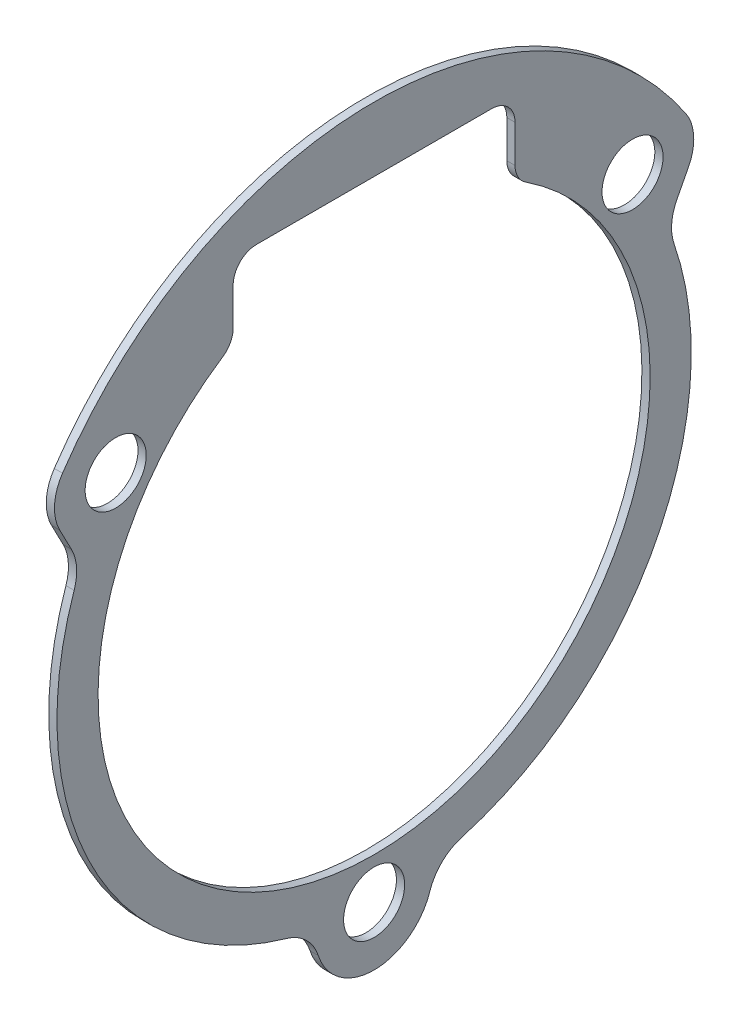
SolidWorks part; units mm, degrees
ref_plane "Front Plane" through (0, 0, 0) normal (0, 0, 1) x (1, 0, 0)
ref_plane "Top Plane" through (0, 0, 0) normal (0, 1, 0) x (1, 0, 0)
ref_plane "Right Plane" through (0, 0, 0) normal (1, 0, 0) x (0, 0, -1)
sketch "Sketch1" plane through (0, 0, 0) normal (1, 0, 0) x (0, 0, -1)
  line L0 (0, -11.75) -> (0, -13.5016) construction
  line L1 (0, 0) -> (-11, 7.8291) construction
  line L2 (-11, 7.8291) -> (11, 7.8291) construction
  line L3 (11, 7.8291) -> (0, 0) construction
  line L4 (-11, 7.8291) -> (0, -13.5016) construction
  line L5 (0, 13.25) -> (0, 0) construction
  line L6 (-5, 13.25) -> (5, 13.25)
  line L7 (-6, 12.25) -> (-6, 10.6566)
  line L8 (0, 0) -> (-11.75, 0) construction
  line L9 (6, 12.25) -> (6, 10.6566)
  line L10 (0, 0) -> (11.75, 0) construction
  line L11 (0, 0) -> (0, -11.75) construction
  line L12 (11.75, 0) -> (13.5, 0) construction
  line L13 (-11.75, 0) -> (-13.5, 0) construction
  line L14 (-12.8858, 5.9536) -> (-13.3811, 6.9071)
  line L15 (12.8858, 5.9536) -> (13.3811, 6.9071)
  line L16 (0, 13.25) -> (0, 16) construction
  arc A0 (-6.451, 9.8208) -> (6.451, 9.8208) centre (0, 0) ccw
  arc A1 (13.2643, 8.9475) -> (-13.2643, 8.9475) centre (0, 0) ccw
  arc A2 (-12.7689, 4.3824) -> (-3.7259, -12.9757) centre (0, 0) ccw
  circle A3 centre (11, 7.8291) radius 1.3
  circle A4 centre (-11, 7.8291) radius 1.3
  circle A5 centre (0, -13.5016) radius 1.3
  circle A6 centre (0, 0) radius 13.5016 construction
  arc A7 (-6, 10.6566) -> (-6.451, 9.8208) centre (-7, 10.6566) cw
  arc A8 (-5, 13.25) -> (-6, 12.25) centre (-5, 12.25) ccw
  arc A9 (6, 12.25) -> (5, 13.25) centre (5, 12.25) ccw
  arc A10 (6.451, 9.8208) -> (6, 10.6566) centre (7, 10.6566) cw
  arc A11 (12.7689, 4.3824) -> (12.8858, 5.9536) centre (14.6606, 5.0316) cw
  arc A12 (3.7259, -12.9757) -> (12.7689, 4.3824) centre (0, 0) ccw
  arc A13 (-2.3766, -14.2774) -> (2.3766, -14.2774) centre (0, -13.5016) ccw
  arc A14 (-12.7689, 4.3824) -> (-12.8858, 5.9536) centre (-14.6606, 5.0316) ccw
  arc A15 (13.2643, 8.9475) -> (13.3811, 6.9071) centre (11.6063, 7.8291) cw
  arc A16 (-13.3811, 6.9071) -> (-13.2643, 8.9475) centre (-11.6063, 7.8291) cw
  arc A17 (-2.3766, -14.2774) -> (-3.7259, -12.9757) centre (-4.2779, -14.898) ccw
  arc A18 (3.7259, -12.9757) -> (2.3766, -14.2774) centre (4.2779, -14.898) ccw
  dimension "D3" = 2.6
  dimension "D4" = 1
  dimension "D9" = 2
  dimension "D10" = 2.5
  dimension "D11" = 16
  dimension "D1" = 22
  dimension "D2" = 24
  dimension "D5" = 12
  dimension "D6" = 23.5
  dimension "D7" = 25
  dimension "D8" = 27
extrude "Extrude1" add sketch "Sketch1" along normal blind 0.35
